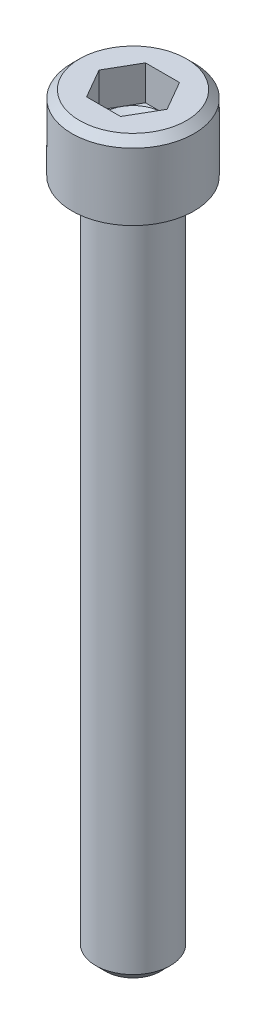
SolidWorks part; units mm, degrees
material "Alloy Steel"
ref_plane "Front Plane" through (0, 0, 0) normal (0, 0, 1) x (1, 0, 0)
ref_plane "Top Plane" through (0, 0, 0) normal (0, 1, 0) x (1, 0, 0)
ref_plane "Right Plane" through (0, 0, 0) normal (1, 0, 0) x (0, 0, -1)
sketch "Sketch1" plane through (0, 0, 0) normal (0, 0, 1) x (1, 0, 0)
  line L0 (2.8702, 3.5052) -> (0, 3.5052)
  line L1 (0, 3.5052) -> (0, 0)
  line L2 (0, 0) -> (2.8702, 0)
  line L3 (2.8702, 0) -> (2.8702, 3.5052)
  line L4 (0, 3.5052) -> (0, 0) construction
revolve "Revolve1" add sketch "Sketch1" angle 360 about L4
sketch "Sketch2" plane through (0, 0, 0) normal (0, -1, 0) x (1, 0, 0)
  circle A0 centre (0, 0) radius 1.7526
extrude "Boss-Extrude1" add sketch "Sketch2" along normal blind 31.75
sketch "Sketch3" plane through (0, 3.5052, 0) normal (0, 1, 0) x (-1, 0, 0)
  line L0 (-0.7992, 1.3843) -> (-1.5985, 0)
  line L1 (-1.5985, 0) -> (-0.7992, -1.3843)
  line L2 (-0.7992, -1.3843) -> (0.7992, -1.3843)
  line L3 (0.7992, -1.3843) -> (1.5985, 0)
  line L4 (1.5985, 0) -> (0.7992, 1.3843)
  line L5 (0.7992, 1.3843) -> (-0.7992, 1.3843)
extrude "Cut-Extrude1" cut sketch "Sketch3" against normal blind 1.6256
sketch "Sketch4" plane through (0, 0, 0) normal (0, 0, 1) x (1, 0, 0)
  line L0 (1.3843, 1.8796) -> (0, 1.8796)
  line L1 (0, 1.8796) -> (0, 1.0804)
  line L2 (0, 1.0804) -> (1.3843, 1.8796)
  line L3 (0, 1.8796) -> (0, 1.0803) construction
revolve "Cut-Revolve1" cut sketch "Sketch4" angle 360 about L3
chamfer "Chamfer1" distance 0.4724 angle 45 1 edges at (0, -31.75, -1.7526)
chamfer "Chamfer2" distance 0.3556 angle 45 1 edges at (0, 3.5052, -2.8702)
fillet "Fillet1" radius 0.254 1 edges at (0, 0, -1.7526)
